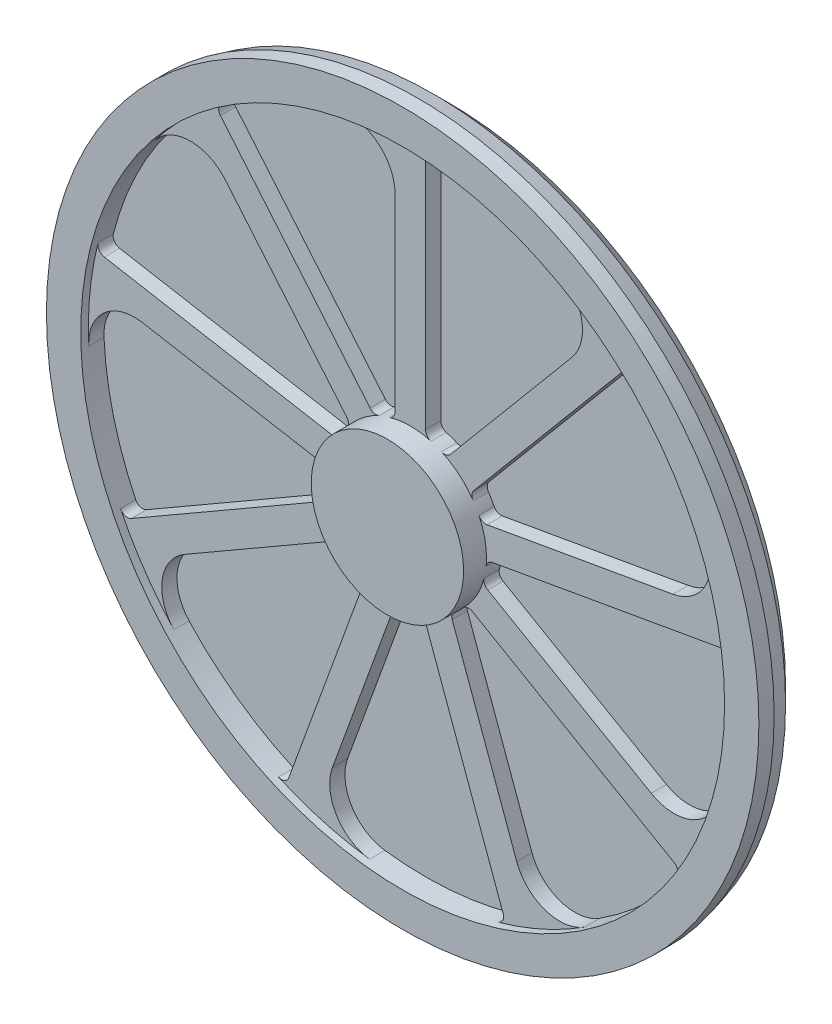
SolidWorks part; units mm, degrees
material "1060 Alloy"
ref_plane "Front Plane" through (0, 0, 0) normal (0, 0, 1) x (1, 0, 0)
ref_plane "Top Plane" through (0, 0, 0) normal (0, 1, 0) x (1, 0, 0)
ref_plane "Right Plane" through (0, 0, 0) normal (1, 0, 0) x (0, 0, -1)
sketch "Sketch1" plane through (0, 0, 0) normal (1, 0, 0) x (0, 0, -1)
  line L0 (0, 0) -> (80, 0)
  line L1 (80, 0) -> (80, 442.5)
  line L2 (80, 442.5) -> (60.4904, 462.0096)
  line L3 (60.4904, 462.0096) -> (40, 467.5)
  line L4 (40, 467.5) -> (20, 467.5)
  line L5 (20, 467.5) -> (20, 422.5)
  line L6 (20, 422.5) -> (50, 422.5)
  line L7 (50, 422.5) -> (50, 100)
  line L8 (50, 100) -> (0, 100)
  line L9 (0, 100) -> (0, 0)
  point P3 (0, 0)
  point P12 (0, 0)
  point P13 (20, 409.1714)
  point P14 (40, 468.3233)
  dimension "D1" = 80
  dimension "D2" = 100
  dimension "D3" = 442.5
  dimension "D4" = 30
  dimension "D5" = 60
  dimension "D6" = 45
  dimension "D7" = 20
  dimension "D8" = 45
  dimension "D9" = 467.5
  dimension "D10" = 15
revolve "Revolve1" add sketch "Sketch1" angle 360 about L0
sketch "Sketch2" plane through (0, 0, -50) normal (0, 0, 1) x (1, 0, 0)
  line L0 (0, 496.1419) -> (0, -505.2694) construction
  line L1 (20, 411.4076) -> (20, 105.8301)
  line L2 (-20, 353.5622) -> (-20, 105.8301)
  line L3 (211.9445, 283.7001) -> (52.7054, 93.9263)
  line L4 (279.7686, 302.3008) -> (83.3471, 68.2148)
  line L5 (344.7179, 81.0916) -> (100.7493, 38.0734)
  line L6 (408.6304, 51.744) -> (107.6952, -1.319)
  line L7 (316.1939, -159.4606) -> (101.6515, -35.5945)
  line L8 (346.2895, -223.0243) -> (81.6515, -70.2355)
  line L9 (139.7193, -325.3994) -> (54.9899, -92.6073)
  line L10 (121.9158, -393.4371) -> (17.4022, -106.2881)
  line L11 (-102.1316, -339.0802) -> (-17.4022, -106.2881)
  line L12 (-159.5036, -379.7563) -> (-54.9899, -92.6073)
  line L13 (-296.1939, -194.1016) -> (-81.6515, -70.2355)
  line L14 (-366.2895, -188.3833) -> (-101.6515, -35.5945)
  line L15 (-351.6638, 41.6993) -> (-107.6952, -1.319)
  line L16 (-401.6845, 91.1363) -> (-100.7493, 38.0734)
  line L17 (-242.5863, 257.9886) -> (-83.3471, 68.2148)
  line L18 (-249.1268, 328.0123) -> (-52.7054, 93.9263)
  circle A0 centre (0, 0) radius 422.5 construction
  circle A1 centre (0, 0) radius 100 construction
  circle A2 centre (0, 0) radius 422.5
  circle A3 centre (0, 0) radius 100
  arc A4 (20, 105.8301) -> (27.2727, 96.2091) centre (30, 105.8301) ccw
  arc A5 (-20, 353.5622) -> (-93.2414, 412.0829) centre (-80, 353.5622) ccw
  arc A6 (-27.2727, 96.2091) -> (-20, 105.8301) centre (-30, 105.8301) ccw
  arc A7 (30.7273, 421.3812) -> (20, 411.4076) centre (30, 411.4076) ccw
  arc A8 (211.9445, 283.7001) -> (193.4547, 375.6082) centre (165.9819, 322.2674) ccw
  arc A9 (40.9499, 91.231) -> (52.7054, 93.9263) centre (45.0449, 100.3542) ccw
  arc A10 (83.3471, 68.2148) -> (82.7342, 56.1699) centre (91.0076, 61.7869) ccw
  arc A11 (294.397, 303.0456) -> (279.7686, 302.3008) centre (287.4291, 295.8729) ccw
  arc A12 (344.7179, 81.0916) -> (389.6312, 163.3823) centre (334.299, 140.1801) ccw
  arc A13 (90.0116, 43.5649) -> (100.7493, 38.0734) centre (99.0128, 47.9214) ccw
  arc A14 (107.6952, -1.319) -> (99.4834, -10.1519) centre (109.4317, -11.167) ccw
  arc A15 (420.3152, 42.9116) -> (408.6304, 51.744) centre (410.3669, 41.896) ccw
  arc A16 (316.1939, -159.4606) -> (403.4949, -125.292) centre (346.1939, -107.4991) ccw
  arc A17 (96.9559, -24.4857) -> (101.6515, -35.5945) centre (106.6515, -26.9343) ccw
  arc A18 (81.6515, -70.2355) -> (69.6832, -71.7234) centre (76.6515, -78.8958) ccw
  arc A19 (349.5632, -237.3012) -> (346.2895, -223.0243) centre (341.2895, -231.6846) ccw
  arc A20 (139.7193, -325.3994) -> (228.5589, -355.3408) centre (196.1008, -304.8782) ccw
  arc A21 (58.5334, -81.0792) -> (54.9899, -92.6073) centre (64.3868, -89.1871) ccw
  arc A22 (17.4022, -106.2881) -> (7.2775, -99.7348) centre (8.0052, -109.7083) ccw
  arc A23 (115.2467, -406.4781) -> (121.9158, -393.4371) centre (112.5189, -396.8573) ccw
  arc A24 (-102.1316, -339.0802) -> (-53.3224, -419.1217) centre (-45.75, -359.6014) ccw
  arc A25 (-7.2775, -99.7348) -> (-17.4022, -106.2881) centre (-8.0052, -109.7083) ccw
  arc A26 (-54.9899, -92.6073) -> (-58.5334, -81.0792) centre (-64.3868, -89.1871) ccw
  arc A27 (-172.995, -385.4594) -> (-159.5036, -379.7563) centre (-168.9005, -376.3361) ccw
  arc A28 (-296.1939, -194.1016) -> (-310.2535, -286.7908) centre (-266.1939, -246.0631) ccw
  arc A29 (-69.6832, -71.7234) -> (-81.6515, -70.2355) centre (-76.6515, -78.8958) ccw
  arc A30 (-101.6515, -35.5945) -> (-96.9559, -24.4857) centre (-106.6515, -26.9343) ccw
  arc A31 (-380.2904, -184.08) -> (-366.2895, -188.3833) centre (-371.2895, -179.7231) ccw
  arc A32 (-351.6638, 41.6993) -> (-422.0136, -20.2674) centre (-362.0827, -17.3892) ccw
  arc A33 (-99.4834, -10.1519) -> (-107.6952, -1.319) centre (-109.4317, -11.167) ccw
  arc A34 (-100.7493, 38.0734) -> (-90.0116, 43.5649) centre (-99.0128, 47.9214) ccw
  arc A35 (-409.6437, 103.4325) -> (-401.6845, 91.1363) centre (-399.948, 100.9844) ccw
  arc A36 (-242.5863, 257.9886) -> (-336.3088, 255.7394) centre (-288.549, 219.4214) ccw
  arc A37 (-82.7342, 56.1699) -> (-83.3471, 68.2148) centre (-91.0076, 61.7869) ccw
  arc A38 (-52.7054, 93.9263) -> (-40.9499, 91.231) centre (-45.0449, 100.3542) ccw
  arc A39 (-247.3201, 342.5478) -> (-249.1268, 328.0123) centre (-241.4664, 334.4402) ccw
  point P14 (0, 0)
  point P120 (0, 0)
  circle M57 centre (0, 0) radius 100
  circle M58 centre (0, 0) radius 422.5
  dimension "D2" = 10
  dimension "D3" = 60
  dimension "D1" = 40
  dimension "D5" = 40
  dimension "D4" = 9
extrude "Boss-Extrude1" add sketch "Sketch2" along normal blind 20 contours L0 A5 L2 A6 A3 M58 | A2 L0 A4 L1 A7 M57 | A11 A2 A8 L3 A9 A3 A10 L4 | A15 A2 A12 L5 A13 A3 A14 L6 | A19 A2 A16 L7 A17 A3 A18 L8 | A39 A2 A36 L17 A37 A3 A38 L18 | A35 A2 A32 L15 A33 A3 A34 L16 | A31 A2 A28 L13 A29 A3 A30 L14 | A27 A2 A24 L11 A25 A3 A26 L12 | A23 A2 A20 L9 A21 A3 A22 L10
equation "\"A\"= 60"
equation "\"B\"= 935"
equation "\"D1@Sketch1\"=\"A\"+20"
equation "\"D3@Sketch1\"=\"B\"/2-25"
equation "\"D5@Sketch1\"=\"A\""
equation "\"D9@Sketch1\"=\"B\"/2"
